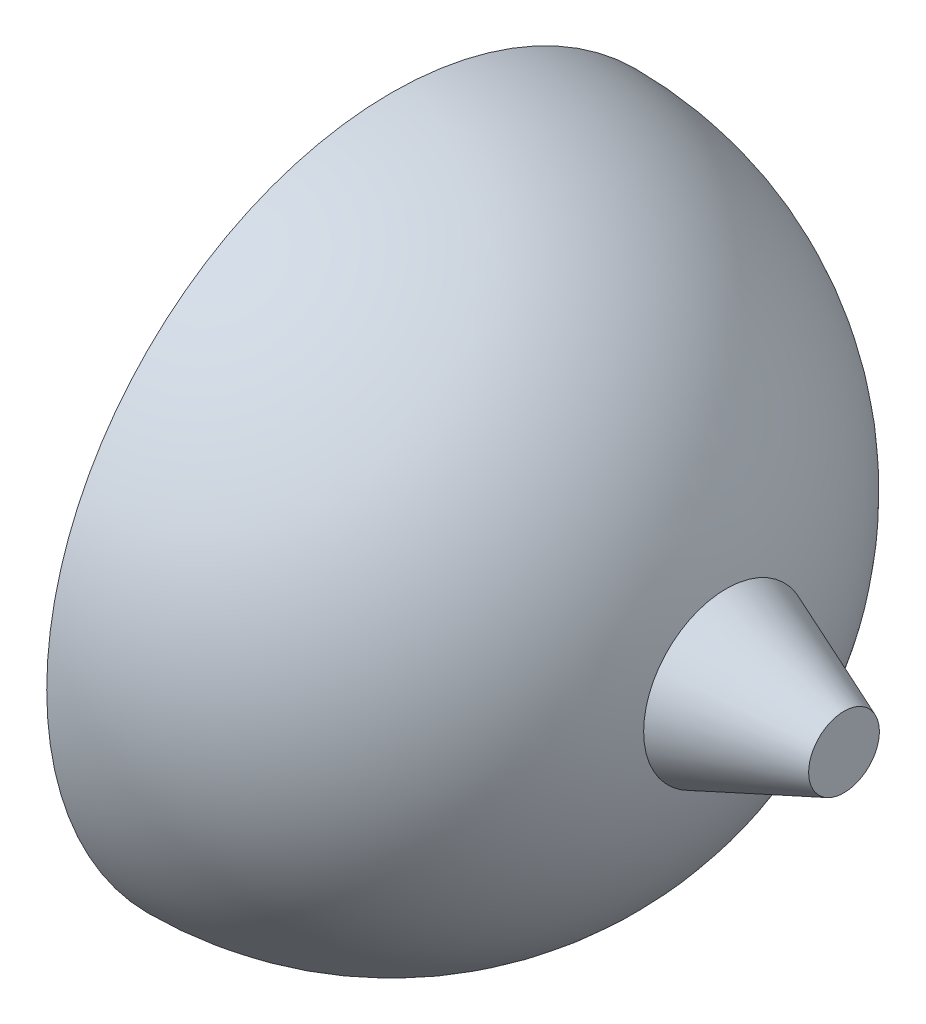
SolidWorks part; units mm, degrees
ref_plane "Front Plane" through (0, 0, 0) normal (0, 0, 1) x (1, 0, 0)
ref_plane "Top Plane" through (0, 0, 0) normal (0, 1, 0) x (1, 0, 0)
ref_plane "Right Plane" through (0, 0, 0) normal (1, 0, 0) x (0, 0, -1)
sketch "Sketch2" plane through (0, 0, 0) normal (0, 1, 0) x (1, 0, 0)
  line L0 (0, 2.925) -> (0, 0.7)
  line L1 (0, 0) -> (-1, 0)
  line L2 (-1, 0) -> (-1, 0.3)
  line L3 (-1, 0.3) -> (0, 0.7)
  line L4 (0, 0) -> (2.925, 0)
  arc A0 (2.925, 0) -> (0, 2.925) centre (0, 0) ccw
  dimension "D1" = 5.85
  dimension "D2" = 1
  dimension "D3" = 0.7
  dimension "D4" = 0.3
revolve "Revolve2" add sketch "Sketch2" angle 360 about L4
sketch "Sketch3" plane through (0, 0, 0) normal (0, 0, 1) x (1, 0, 0)
  line L0 (2.925, 0) -> (3.84, 0)
  line L1 (3.84, 0) -> (3.84, 0.3)
  line L2 (3.84, 0.3) -> (2.84, 0.7)
  line L3 (2.84, 0.7) -> (2.925, 0)
  arc A0 (0, -2.925) -> (0, 2.925) centre (0, 0) ccw construction
  dimension "D1" = 0.3
  dimension "D2" = 0.7
  dimension "D3" = 1
revolve "Revolve3" add sketch "Sketch3" angle 360 about L0
